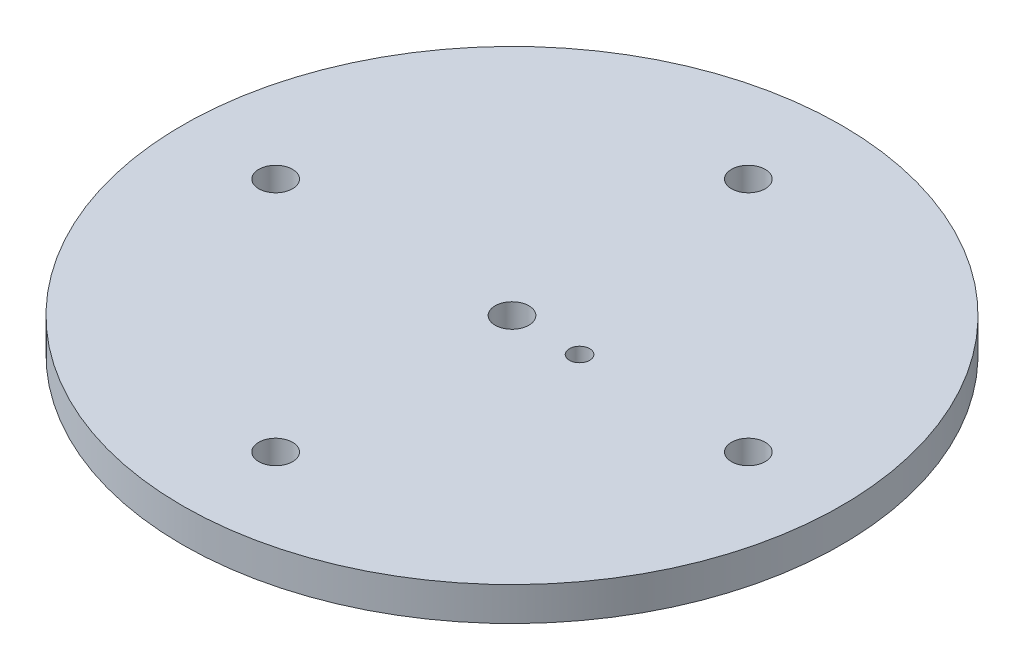
SolidWorks part; units mm, degrees
ref_plane "Front Plane" through (0, 0, 0) normal (0, 0, 1) x (1, 0, 0)
ref_plane "Top Plane" through (0, 0, 0) normal (0, 1, 0) x (1, 0, 0)
ref_plane "Right Plane" through (0, 0, 0) normal (1, 0, 0) x (0, 0, -1)
sketch "Sketch1" plane through (0, 0, 0) normal (0, 1, 0) x (1, 0, 0)
  line L0 (0, 0) -> (0, 44.45)
  line L1 (0, 0) -> (44.45, 0)
  line L2 (0, 0) -> (0, -44.45)
  line L3 (0, 0) -> (-44.45, 0)
  circle A0 centre (0, 0) radius 61.976
  point P10 (0, 0)
  dimension "D1" = 123.952
  dimension "D2" = 44.45
  dimension "D3" = 4
extrude "Boss-Extrude1" add sketch "Sketch1" along normal blind 6.35
hole_wizard "1/4 (0.25) Diameter Hole1" positions "Sketch2" profile "Sketch3" hole size "1/4" standard "ANSI Inch"
sketch "Sketch2" plane through (0, 6.35, 0) normal (0, 1, 0) x (1, 0, 0)
  point P0 (0, 44.45)
  point P3 (44.45, 0)
  point P6 (0, -44.45)
  point P9 (-44.45, 0)
  point P13 (0, 0)
sketch "Sketch3" plane through (0, 6.35, -44.45) normal (1, 0, 0) x (0, 0, 1)
  line L0 (0, 0) -> (0, 44.958)
  line L1 (0, 44.958) -> (3.175, 44.958)
  line L2 (3.175, 44.958) -> (3.175, 0)
  line L5 (3.175, 0) -> (0, 0)
  line L10 (0, 44.958) -> (-3.175, 44.958) construction
  line L11 (0, -6.35) -> (0, 107.95) construction
  dimension "Hole Dia." = 6.35
  dimension "Hole Depth" = 44.958
  dimension "Drill Angle" = 180
sketch "Sketch4" plane through (0, 6.35, 0) normal (0, 1, 0) x (1, 0, 0)
  circle A0 centre (12.7, 0) radius 1.905
  dimension "D1" = 3.81
  dimension "D2" = 12.7
extrude "Cut-Extrude1" cut sketch "Sketch4" against normal through all
